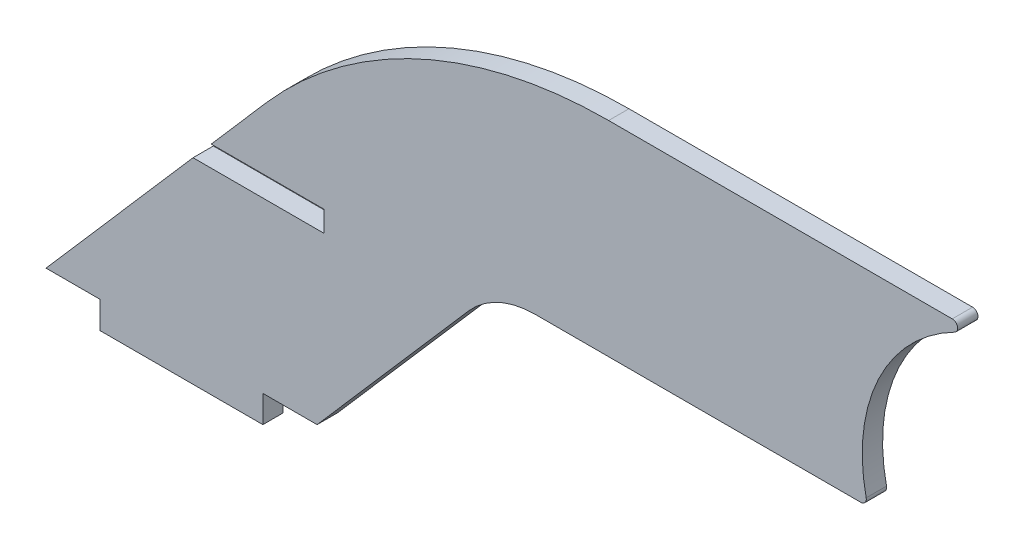
SolidWorks part; units mm, degrees
ref_plane "Front Plane" through (0, 0, 0) normal (0, 0, 1) x (1, 0, 0)
ref_plane "Top Plane" through (0, 0, 0) normal (0, 1, 0) x (1, 0, 0)
ref_plane "Right Plane" through (0, 0, 0) normal (1, 0, 0) x (0, 0, -1)
sketch "Sketch1" plane through (0, 0, 0) normal (0, 0, 1) x (1, 0, 0)
  line L3 (-20, 4) -> (-12, 4)
  line L4 (-20, 4) -> (32.4847, 64.3768)
  line L9 (42.3542, 29.7155) -> (20, 4)
  line L10 (32.4847, 64.3768) -> (113.721, 64.3768)
  line L12 (100.241, 34.1868) -> (52.1654, 34.1868)
  line L15 (-12, 4) -> (-12, 0)
  line L16 (-12, 0) -> (12, 0)
  line L17 (12, 4) -> (12, 0)
  line L18 (0, 0) -> (0, 10.0059) construction
  line L19 (12, 4) -> (20, 4)
  arc A2 (114.086, 62.8649) -> (101.0224, 35.1581) centre (125.5346, 40.5338) ccw
  arc A3 (101.0224, 35.1581) -> (100.241, 34.1868) centre (100.241, 34.9868) cw
  arc A4 (113.721, 64.3768) -> (114.086, 62.8649) centre (113.721, 63.5768) cw
  arc A6 (63.0184, 64.3768) -> (12.4528, 41.3327) centre (63.0184, -2.6232) ccw
  arc A7 (42.3542, 29.7155) -> (52.1654, 34.1868) centre (52.1654, 21.1868) cw
  point P3 (0, 0)
  point P23 (46.241, 34.1868)
  dimension "D2" = 30.19
  dimension "D5" = 0.8
  dimension "D7" = 25.0948
  dimension "D10" = 81.2363
  dimension "D8" = 4
  dimension "D11" = 54
  dimension "D12" = 67
  dimension "D13" = 13
  dimension "D1" = 80
  dimension "D4" = 49
  dimension "D6" = 24
  dimension "D9" = 8
  dimension "D3" = 40
extrude "Boss-Extrude1" add sketch "Sketch1" along normal blind 3
sketch "Sketch2" plane through (0, 0, 3) normal (0, 0, 1) x (1, 0, 0)
  line L4 (21, 30.5) -> (16.7212, 30.5) construction
  line L8 (-10.5413, 28.96) -> (21, 28.96)
  line L9 (21, 28.96) -> (21, 32.04)
  line L10 (21, 32.04) -> (-10.5413, 32.04)
  line L11 (-10.5413, 32.04) -> (-10.5413, 28.96)
  dimension "D2" = 3.08
  dimension "D1" = 31.5413
  dimension "D3" = 28.96
  dimension "D4" = 21.3542
extrude "Cut-Extrude1" cut sketch "Sketch2" against normal up to surface (3 mm away) up to face at (42.2989, 27.9238, 0)
